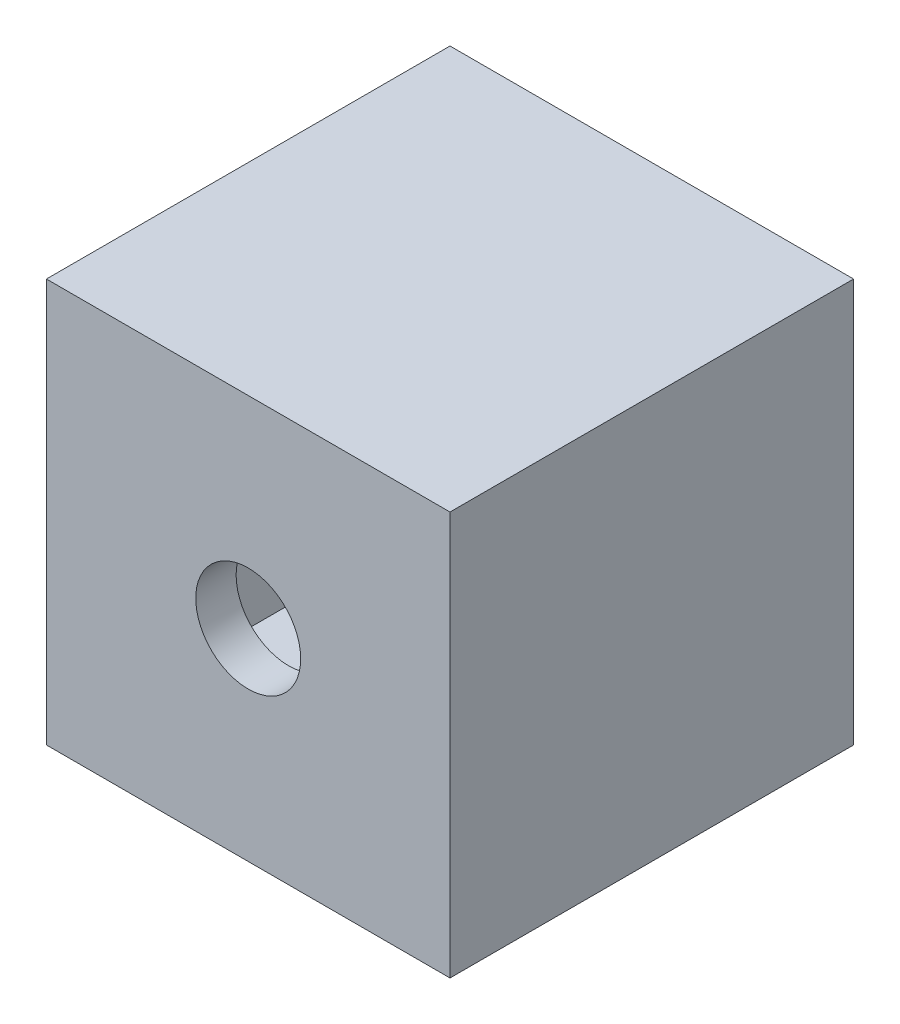
SolidWorks part; units mm, degrees
material "Beech"
ref_plane "Front Plane" through (0, 0, 0) normal (0, 0, 1) x (1, 0, 0)
ref_plane "Top Plane" through (0, 0, 0) normal (0, 1, 0) x (1, 0, 0)
ref_plane "Right Plane" through (0, 0, 0) normal (1, 0, 0) x (0, 0, -1)
sketch "Sketch5" plane through (0, 0, 0) normal (0, 0, 1) x (1, 0, 0)
  line L1 (-100, -100) -> (100, -100)
  line L2 (-100, -100) -> (-100, 100)
  line L3 (-100, 100) -> (100, 100)
  line L4 (100, -100) -> (100, 100)
  line L5 (-100, -100) -> (100, 100) construction
  line L6 (-100, 100) -> (100, -100) construction
  point P0 (0, 0)
  dimension "D1" = 200
  dimension "D2" = 200
extrude "Boss-Extrude2" add sketch "Sketch5" along normal blind 200
shell "Shell2" thickness 20
sketch "Sketch6" plane through (0, 0, 200) normal (0, 0, 1) x (1, 0, 0)
  circle A0 centre (0, 0) radius 26
  dimension "D1" = 52
extrude "Cut-Extrude2" cut sketch "Sketch6" against normal blind 51.6
